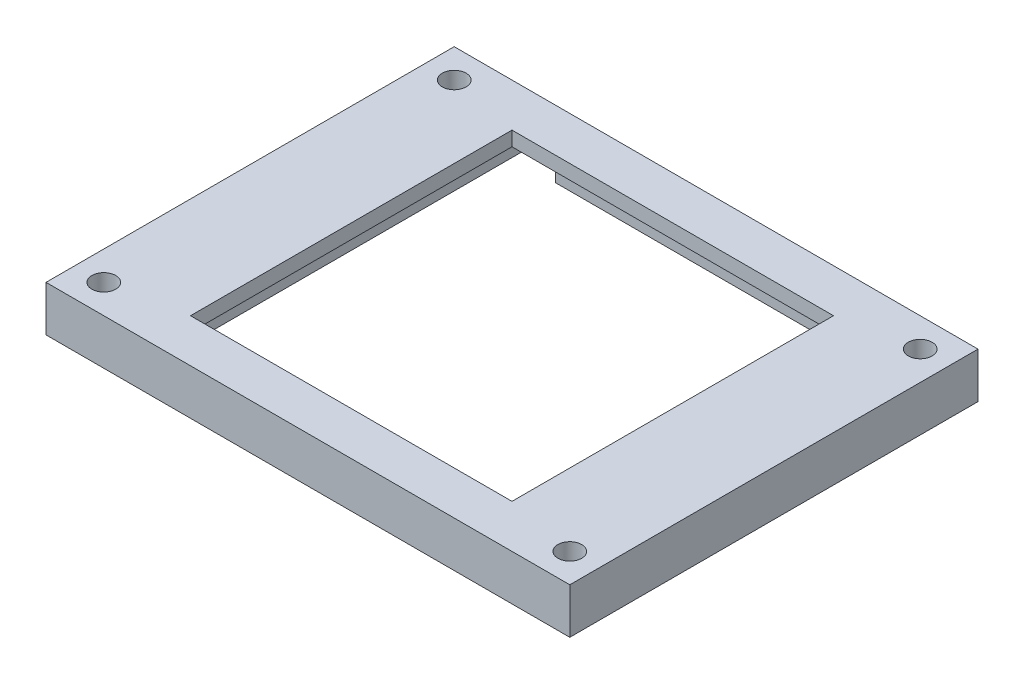
SolidWorks part; units mm, degrees
ref_plane "Front Plane" through (0, 0, 0) normal (0, 0, 1) x (1, 0, 0)
ref_plane "Top Plane" through (0, 0, 0) normal (0, 1, 0) x (1, 0, 0)
ref_plane "Right Plane" through (0, 0, 0) normal (1, 0, 0) x (0, 0, -1)
sketch "Sketch1" plane through (0, 0, 0) normal (0, 1, 0) x (1, 0, 0)
  line L0 (-28.25, 12.25) -> (-36.25, 20.25)
  line L1 (-25.25, 25.25) -> (25.25, 25.25)
  line L2 (-25.25, 25.25) -> (-25.25, -25.25)
  line L3 (-25.25, -25.25) -> (25.25, -25.25)
  line L4 (25.25, 25.25) -> (25.25, -25.25)
  line L5 (-25.25, 25.25) -> (25.25, -25.25) construction
  line L6 (-25.25, -25.25) -> (25.25, 25.25) construction
  line L7 (-28.25, 28.25) -> (28.25, 28.25)
  line L8 (-28.25, 28.25) -> (-28.25, -28.25)
  line L9 (-28.25, -28.25) -> (28.25, -28.25)
  line L10 (28.25, 28.25) -> (28.25, -28.25)
  line L11 (-28.25, 28.25) -> (28.25, -28.25) construction
  line L12 (-28.25, -28.25) -> (28.25, 28.25) construction
  line L13 (-36.25, 20.25) -> (-36.25, 30.25)
  line L14 (-36.25, 30.25) -> (-32.25, 34.25)
  line L15 (-32.25, 34.25) -> (-24.25, 34.25)
  line L16 (-24.25, 34.25) -> (-18.25, 28.25)
  line L17 (-55, 0) -> (55, 0) construction
  line L18 (-28.25, -12.25) -> (-36.25, -20.25)
  line L19 (-24.25, -34.25) -> (-18.25, -28.25)
  line L20 (-32.25, -34.25) -> (-24.25, -34.25)
  line L21 (-36.25, -30.25) -> (-32.25, -34.25)
  line L22 (-36.25, -20.25) -> (-36.25, -30.25)
  line L23 (0, -55) -> (0, 55) construction
  line L24 (32.25, -34.25) -> (24.25, -34.25)
  line L25 (24.25, -34.25) -> (18.25, -28.25)
  line L26 (28.25, -12.25) -> (36.25, -20.25)
  line L27 (36.25, -20.25) -> (36.25, -30.25)
  line L28 (36.25, -30.25) -> (32.25, -34.25)
  line L29 (24.25, 34.25) -> (18.25, 28.25)
  line L30 (32.25, 34.25) -> (24.25, 34.25)
  line L31 (36.25, 30.25) -> (32.25, 34.25)
  line L32 (36.25, 20.25) -> (36.25, 30.25)
  line L33 (28.25, 12.25) -> (36.25, 20.25)
  circle A0 centre (-32.25, 24.25) radius 1.65
  circle A1 centre (-32.25, -24.25) radius 1.65
  circle A2 centre (32.25, -24.25) radius 1.65
  circle A3 centre (32.25, 24.25) radius 1.65
  point P0 (0, 0)
  point P5 (0, 0)
  dimension "D11" = 3.3
  dimension "D12" = 4
  dimension "D1" = 50.5
  dimension "D2" = 50.5
  dimension "D3" = 56.5
  dimension "D4" = 6
  dimension "D5" = 8
  dimension "D6" = 4
  dimension "D7" = 8
  dimension "D8" = 4
  dimension "D9" = 4
  dimension "D10" = 45
  dimension "D13" = 4
extrude "Boss-Extrude1" add sketch "Sketch1" along normal blind 8.6 contours L10 L7 L8 L9 L1 L4 L3 L2 | L18 L22 L21 L20 L19 L9 L8 A1 | L28 L27 L26 L10 L9 L25 L24 A2 | L10 L33 L32 L31 L30 L29 L7 A3 | L16 L15 L14 L13 L0 L8 L7 A0
sketch "Sketch2" plane through (0, 0, 0) normal (0, 1, 0) x (1, 0, 0)
  line L1 (-25.25, 25.25) -> (25.25, 25.25)
  line L2 (-25.25, 25.25) -> (-25.25, -25.25)
  line L3 (-25.25, -25.25) -> (25.25, -25.25)
  line L4 (25.25, 25.25) -> (25.25, -25.25)
  line L5 (-25.25, 25.25) -> (25.25, -25.25) construction
  line L6 (-25.25, -25.25) -> (25.25, 25.25) construction
  line L7 (-22.25, 22.25) -> (22.25, 22.25)
  line L8 (-22.25, 22.25) -> (-22.25, -22.25)
  line L9 (-22.25, -22.25) -> (22.25, -22.25)
  line L10 (22.25, 22.25) -> (22.25, -22.25)
  line L11 (-22.25, 22.25) -> (22.25, -22.25) construction
  line L12 (-22.25, -22.25) -> (22.25, 22.25) construction
  point P0 (0, 0)
  point P5 (0, 0)
  dimension "D1" = 50.5
  dimension "D2" = 50.5
  dimension "D3" = 44.5
  dimension "D4" = 44.5
extrude "Boss-Extrude2" add sketch "Sketch2" along normal blind 2
sketch "Sketch4" plane through (0, 0, 0) normal (0, 1, 0) x (1, 0, 0)
  line L1 (-25.25, 25.25) -> (25.25, 25.25)
  line L2 (-25.25, 25.25) -> (-25.25, -25.25)
  line L3 (-25.25, -25.25) -> (25.25, -25.25)
  line L4 (25.25, 25.25) -> (25.25, -25.25)
  line L5 (-25.25, 25.25) -> (25.25, -25.25) construction
  line L6 (-25.25, -25.25) -> (25.25, 25.25) construction
  line L7 (-22.25, 22.25) -> (22.25, 22.25)
  line L8 (-22.25, 22.25) -> (-22.25, -22.25)
  line L9 (-22.25, -22.25) -> (22.25, -22.25)
  line L10 (22.25, 22.25) -> (22.25, -22.25)
  line L11 (-22.25, 22.25) -> (22.25, -22.25) construction
  line L12 (-22.25, -22.25) -> (22.25, 22.25) construction
  point P0 (0, 0)
  point P5 (0, 0)
extrude "Boss-Extrude3" add sketch "Sketch4" along normal blind 2 from offset 6.6
sketch "Sketch5" plane through (0, 0, 0) normal (0, 1, 0) x (1, 0, 0)
  line L1 (-25.25, 19.8891) -> (-19.25, 19.8891)
  line L2 (-25.25, 19.8891) -> (-25.25, 37.8505)
  line L3 (-25.25, 37.8505) -> (-19.25, 37.8505)
  line L4 (-19.25, 19.8891) -> (-19.25, 37.8505)
  line L5 (19.25, 19.8891) -> (25.25, 19.8891)
  line L6 (19.25, 19.8891) -> (19.25, 37.8505)
  line L7 (19.25, 37.8505) -> (25.25, 37.8505)
  line L8 (25.25, 19.8891) -> (25.25, 37.8505)
  dimension "D1" = 6
  dimension "D2" = 6
  dimension "D3" = 25.25
  dimension "D4" = 25.25
extrude "Cut-Extrude1" cut sketch "Sketch5" along normal blind 4.6 from offset 2
sketch "Sketch6" plane through (0, 0, 0) normal (0, -1, 0) x (1, 0, 0)
  line L1 (-41.762, 39.56) -> (45.5585, 39.56)
  line L2 (-41.762, 39.56) -> (-41.762, -42.5972)
  line L3 (-41.762, -42.5972) -> (45.5585, -42.5972)
  line L4 (45.5585, 39.56) -> (45.5585, -42.5972)
extrude "Cut-Extrude2" cut sketch "Sketch6" against normal blind 2.3
sketch "Sketch7" plane through (0, 8.6, 0) normal (0, 1, 0) x (1, 0, 0)
  line L0 (-18.25, 28.25) -> (18.25, 28.25) construction
  line L1 (-36.25, 20.25) -> (-28.25, 20.25)
  line L2 (-36.25, 20.25) -> (-36.25, -20.25)
  line L3 (-36.25, -20.25) -> (-28.25, -20.25)
  line L4 (-28.25, 20.25) -> (-28.25, -20.25)
  line L5 (36.25, 20.25) -> (28.25, 20.25)
  line L6 (36.25, 20.25) -> (36.25, -20.25)
  line L7 (36.25, -20.25) -> (28.25, -20.25)
  line L8 (28.25, 20.25) -> (28.25, -20.25)
  line L9 (0, 28.25) -> (-38.2076, 28.25)
  line L10 (0, 28.25) -> (0, 36.7246)
  line L11 (0, 36.7246) -> (-38.2076, 36.7246)
  line L12 (-38.2076, 28.25) -> (-38.2076, 36.7246)
  line L13 (-18.25, -28.25) -> (18.25, -28.25) construction
  line L14 (0, 28.25) -> (40.9812, 28.25)
  line L15 (0, 28.25) -> (0, 36.7246)
  line L16 (0, 36.7246) -> (40.9812, 36.7246)
  line L17 (40.9812, 28.25) -> (40.9812, 36.7246)
  line L18 (0, -28.25) -> (-40.8818, -28.25)
  line L19 (0, -28.25) -> (0, -34.9953)
  line L20 (0, -34.9953) -> (-40.8818, -34.9953)
  line L21 (-40.8818, -28.25) -> (-40.8818, -34.9953)
  line L23 (0, -28.25) -> (39.1843, -28.25)
  line L24 (0, -28.25) -> (0, -34.9953)
  line L25 (0, -34.9953) -> (39.1843, -34.9953)
  line L26 (39.1843, -28.25) -> (39.1843, -34.9953)
  line M1 (28.25, -12.25) -> (28.25, 12.25)
  line M2 (28.25, 12.25) -> (36.25, 20.25)
  line M3 (36.25, 20.25) -> (36.25, 30.25)
  line M4 (36.25, 30.25) -> (32.25, 34.25)
  line M5 (32.25, 34.25) -> (24.25, 34.25)
  line M6 (24.25, 34.25) -> (18.25, 28.25)
  line M7 (18.25, 28.25) -> (-18.25, 28.25)
  line M8 (-18.25, 28.25) -> (-24.25, 34.25)
  line M9 (-24.25, 34.25) -> (-32.25, 34.25)
  line M10 (-32.25, 34.25) -> (-36.25, 30.25)
  line M11 (-36.25, 30.25) -> (-36.25, 20.25)
  line M12 (-36.25, 20.25) -> (-28.25, 12.25)
  line M13 (-28.25, 12.25) -> (-28.25, -12.25)
  line M14 (-28.25, -12.25) -> (-36.25, -20.25)
  line M15 (-36.25, -20.25) -> (-36.25, -30.25)
  line M16 (-36.25, -30.25) -> (-32.25, -34.25)
  line M17 (-32.25, -34.25) -> (-24.25, -34.25)
  line M18 (-24.25, -34.25) -> (-18.25, -28.25)
  line M19 (-18.25, -28.25) -> (18.25, -28.25)
  line M20 (18.25, -28.25) -> (24.25, -34.25)
  line M21 (24.25, -34.25) -> (32.25, -34.25)
  line M22 (32.25, -34.25) -> (36.25, -30.25)
  line M23 (36.25, -30.25) -> (36.25, -20.25)
  line M24 (36.25, -20.25) -> (28.25, -12.25)
extrude "Cut-Extrude4" cut sketch "Sketch7" against normal blind 10 contours L18 L21 L20 L19 M19 M18 M17 M16 M15 | L26 L23 L19 L25 M23 M22 M21 M20 M19 | L6 M2 M1 M24 | L2 M12 M14 M13 | L9 M8 M9 M10 M11 | L12 L9 L10 L11 M11 M10 M9 M8 M7 | L5 L8 M2 | L8 L7 M24 | L18 M18 M15 M16 M17 | L4 L3 M14 | L4 L1 M12 | L14 M6 M3 M4 M5 | L14 L17 L16 L10 M7 M6 M5 M4 M3 | L23 M20 M21 M22 M23
sketch "Sketch8" plane through (0, 8.6, 0) normal (0, 1, 0) x (1, 0, 0)
  line L1 (-36.25, 20.25) -> (-28.25, 20.25)
  line L2 (-36.25, 20.25) -> (-36.25, -20.25)
  line L3 (-36.25, -20.25) -> (-28.25, -20.25)
  line L4 (-28.25, 20.25) -> (-28.25, -20.25)
  line L5 (28.25, -20.25) -> (36.25, -20.25)
  line L6 (28.25, -20.25) -> (28.25, 20.25)
  line L7 (28.25, 20.25) -> (36.25, 20.25)
  line L8 (36.25, -20.25) -> (36.25, 20.25)
extrude "Boss-Extrude4" add sketch "Sketch8" against normal up to vertex (6.3 mm away) up to point (-36.25, 2.3, 20.25)
